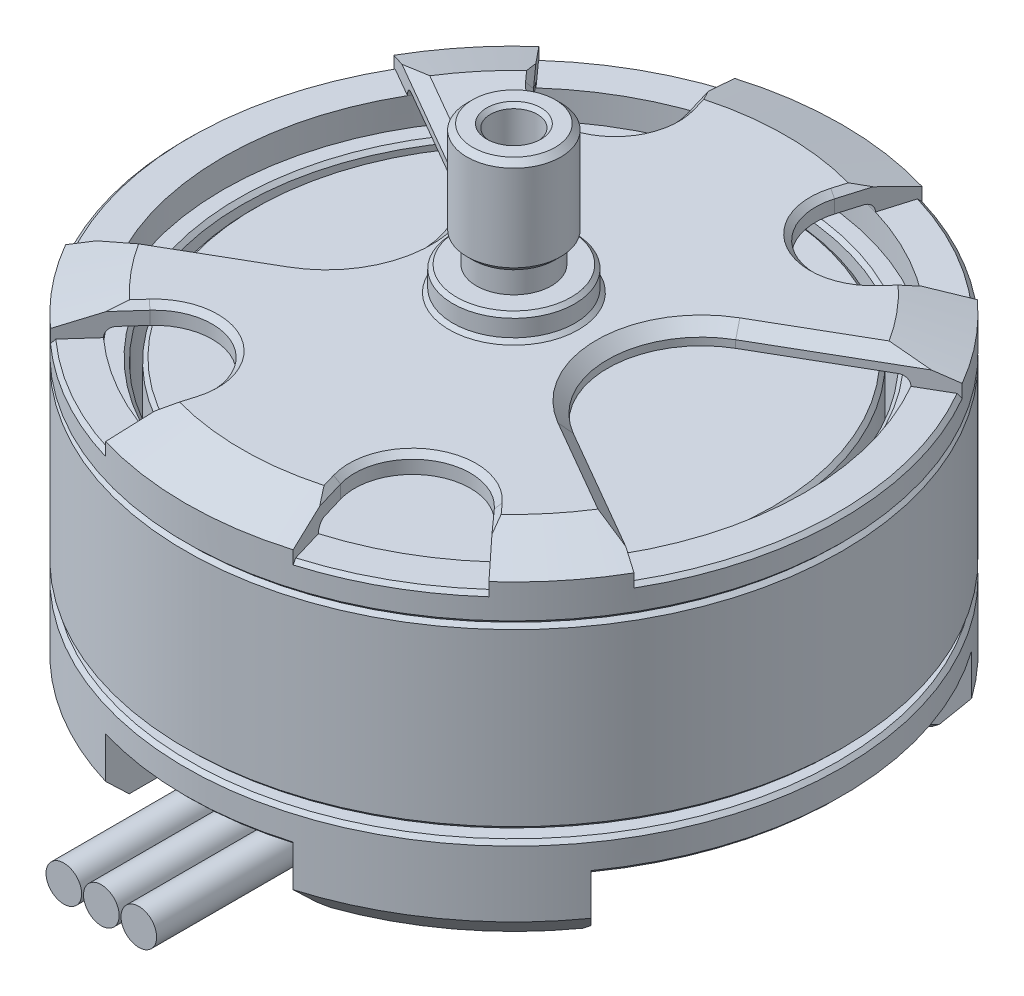
SolidWorks part; units mm, degrees
ref_plane "Front Plane" through (0, 0, 0) normal (0, 0, 1) x (1, 0, 0)
ref_plane "Top Plane" through (0, 0, 0) normal (0, 1, 0) x (1, 0, 0)
ref_plane "Right Plane" through (0, 0, 0) normal (1, 0, 0) x (0, 0, -1)
sketch "Sketch1" plane through (0, 0, 0) normal (0, 0, 1) x (1, 0, 0)
  line L0 (0.75, 0) -> (2, 0)
  line L1 (2, 0) -> (2, 2)
  line L2 (2, 2) -> (5, 2)
  line L3 (5, 2) -> (6, 0)
  line L4 (6, 0) -> (16, 0)
  line L5 (16, 0) -> (17.5, 1.5)
  line L6 (17.5, 1.5) -> (17.5, 5.2)
  line L8 (14, 6.2) -> (14, 15.2)
  line L9 (14, 15.2) -> (3.25, 15.2)
  line L10 (3.25, 15.2) -> (3.25, 17.2)
  line L13 (16, 5.7) -> (17.5, 5.7)
  line L14 (17.5, 5.7) -> (17.5, 17.2) construction
  line L15 (17.5, 17.2) -> (14.5, 18.2)
  line L16 (14.5, 18.2) -> (3.25, 18.2)
  line L17 (3.25, 18.2) -> (3.25, 19.5)
  line L18 (3.25, 19.5) -> (2, 19.5)
  line L20 (2.5, 26) -> (0, 26)
  line L21 (0, 26) -> (0, 18.2)
  line L22 (14, 6.2) -> (6.5, 6.2)
  line L23 (6.5, 6.2) -> (6.5, 3.2)
  line L24 (7.5, 2.2) -> (15, 2.2)
  line L25 (16, 3.2) -> (16, 5.2)
  line L26 (16, 5.2) -> (17.5, 5.2)
  line L27 (3.25, 17.2) -> (15, 17.2)
  line L28 (15.5, 16.7) -> (15.5, 15.2)
  line L29 (15.5, 15.2) -> (14.5, 15.2)
  line L30 (14.5, 15.2) -> (14.5, 6.2)
  line L31 (14.5, 6.2) -> (16, 6.2)
  line L32 (16, 6.2) -> (16, 5.7)
  line L33 (17.5, 17.2) -> (17.5, 15.4)
  line L34 (17.5, 15.4) -> (17.3, 15.2)
  line L35 (17.3, 15.2) -> (17.5, 15)
  line L36 (17.5, 15) -> (17.5, 5.7)
  line L37 (2.5, 26) -> (2.5, 20.8)
  line L38 (2.5, 20.8) -> (2, 20.8)
  line L39 (2, 20.8) -> (2, 19.5)
  line L40 (0, 18.2) -> (0.75, 18.2)
  line L41 (0.75, 18.2) -> (0.75, 0)
  arc A0 (15, 2.2) -> (16, 3.2) centre (15, 3.2) ccw
  arc A1 (15, 17.2) -> (15.5, 16.7) centre (15, 16.7) cw
  arc A2 (6.5, 3.2) -> (7.5, 2.2) centre (7.5, 3.2) ccw
  point P25 (-2, 0)
  point P27 (-2.5, 26)
  point P28 (-3.25, 19.5)
  point P29 (-14.5, 18.2)
  point P30 (-14, 6.2)
  point P31 (-17.5, 5.2)
  point P32 (-5, 2)
  point P46 (-6.5, 2.2)
  point P49 (6.5, 2.2)
  point P50 (-6, 0)
  point P56 (-2, 20.8)
  point P57 (-0.75, 18.2)
  dimension "D20" = 0.5
  dimension "D23" = 1
  dimension "D1" = 4
  dimension "D2" = 35
  dimension "D3" = 135
  dimension "D4" = 2
  dimension "D5" = 10
  dimension "D6" = 5.2
  dimension "D7" = 12.5
  dimension "D8" = 3
  dimension "D9" = 1
  dimension "D10" = 18.2
  dimension "D11" = 1.5
  dimension "D12" = 3
  dimension "D13" = 1
  dimension "D14" = 5
  dimension "D15" = 6.5
  dimension "D16" = 2
  dimension "D17" = 3
  dimension "D18" = 0.5
  dimension "D19" = 2.2
  dimension "D21" = 0.5
  dimension "D22" = 13
  dimension "D24" = 1.3
  dimension "D25" = 26
  dimension "D26" = 0.4
  dimension "D27" = 1.5
  dimension "D28" = 12
  dimension "D29" = 4
  dimension "D30" = 1.5
revolve "Revolve1" add sketch "Sketch1" angle 360 about L21
sketch "Sketch2" plane through (0, 0, 0) normal (0, -1, 0) x (1, 0, 0)
  line L0 (-5, 16.7705) -> (-5, 8.0777)
  line L2 (0, 0) -> (0, 17.5) construction
  line L3 (5, 16.7705) -> (5, 8.0777)
  line L4 (14.2539, 10.1527) -> (8.4475, 4.3463)
  line L5 (8.4475, -4.3463) -> (14.2539, -10.1527)
  line L6 (0, 0) -> (9.5, 0) construction
  line L7 (-4.3463, -8.4475) -> (-10.1527, -14.2539)
  line L8 (10.1527, -14.2539) -> (4.3463, -8.4475)
  line L9 (-8.4475, 4.3463) -> (-14.2539, 10.1527)
  line L10 (-14.2539, -10.1527) -> (-8.4475, -4.3463)
  line L11 (0, 0) -> (8.4475, -4.3463) construction
  line L12 (0, 0) -> (-4.3463, -8.4475) construction
  line L13 (12.3744, 12.3744) -> (-12.3744, -12.3744) construction
  line L14 (-12.3744, 12.3744) -> (12.3744, -12.3744) construction
  line L15 (-12.3744, 12.3744) -> (12.3744, 12.3744) construction
  circle A0 centre (0, 0) radius 17.5 construction
  arc A1 (5, 16.7705) -> (-5, 16.7705) centre (0, 0) ccw
  arc A2 (5, 8.0777) -> (-5, 8.0777) centre (0, 0) ccw
  arc A4 (8.4475, -4.3463) -> (8.4475, 4.3463) centre (0, 0) ccw
  arc A5 (14.2539, 10.1527) -> (14.2539, -10.1527) centre (0, 0) cw
  arc A6 (10.1527, -14.2539) -> (-10.1527, -14.2539) centre (0, 0) cw
  arc A7 (-4.3463, -8.4475) -> (4.3463, -8.4475) centre (0, 0) ccw
  arc A8 (-14.2539, -10.1527) -> (-14.2539, 10.1527) centre (0, 0) cw
  arc A9 (-8.4475, 4.3463) -> (-8.4475, -4.3463) centre (0, 0) ccw
  circle A10 centre (8.8388, 8.8388) radius 1.5
  circle A11 centre (6.7175, -6.7175) radius 1.5
  circle A12 centre (-8.8388, -8.8388) radius 1.5
  circle A13 centre (-6.7175, 6.7175) radius 1.5
  dimension "D2" = 9.5
  dimension "D6" = 3
  dimension "D1" = 10
  dimension "D4" = 90
  dimension "D5" = 5.8
  dimension "D7" = 25
  dimension "D8" = 19
  dimension "D3" = 3
extrude "Cut-Extrude4" cut sketch "Sketch2" against normal blind 3.5
fillet "Fillet1" radius 2 8 edges at (-4.3463, 1.1, -8.4475) (4.3463, 1.1, -8.4475) (-8.4475, 1.1, -4.3463) (-8.4475, 1.1, 4.3463) (8.4475, 1.1, -4.3463) (8.4475, 1.1, 4.3463) (-5, 1.1, 8.0777) (5, 1.1, 8.0777)
sketch "Sketch3" plane through (0, 18.2, 0) normal (0, 1, 0) x (1, 0, 0)
  line L0 (0, 17.5) -> (0, 0) construction
  line L1 (0, 0) -> (17.5, 0) construction
  line L2 (5, 16.7705) -> (3.927, 13.1716)
  line L3 (9.1822, 10.2274) -> (11.6911, 13.0218)
  line L4 (15.1554, 8.75) -> (7.5, 4.3301)
  line L5 (7.5, -4.3301) -> (15.1554, -8.75)
  line L6 (9.1822, -10.2274) -> (11.6911, -13.0218)
  line L7 (5, -16.7705) -> (3.927, -13.1716)
  line L8 (-9.1822, 10.2274) -> (-11.6911, 13.0218)
  line L9 (-5, 16.7705) -> (-3.927, 13.1716)
  line L10 (-7.5, -4.3301) -> (-15.1554, -8.75)
  line L11 (-15.1554, 8.75) -> (-7.5, 4.3301)
  line L12 (-9.1822, -10.2274) -> (-11.6911, -13.0218)
  line L13 (-5, -16.7705) -> (-3.927, -13.1716)
  line L14 (5.3765, 9.5965) -> (-5.3765, -9.5965) construction
  circle A0 centre (0, 0) radius 17.5 construction
  arc A1 (3.927, 13.1716) -> (9.1822, 10.2274) centre (6.8852, 12.2896) ccw
  arc A2 (7.5, 4.3301) -> (7.5, -4.3301) centre (10, 0) ccw
  arc A3 (15.1554, -8.75) -> (15.1554, 8.75) centre (0, 0) ccw
  arc A4 (11.6911, 13.0218) -> (5, 16.7705) centre (0, 0) ccw
  arc A5 (11.6911, -13.0218) -> (5, -16.7705) centre (0, 0) cw
  arc A6 (3.927, -13.1716) -> (9.1822, -10.2274) centre (6.8852, -12.2896) cw
  arc A7 (-11.6911, 13.0218) -> (-5, 16.7705) centre (0, 0) cw
  arc A8 (-3.927, 13.1716) -> (-9.1822, 10.2274) centre (-6.8852, 12.2896) cw
  arc A9 (-7.5, 4.3301) -> (-7.5, -4.3301) centre (-10, 0) cw
  arc A10 (-15.1554, -8.75) -> (-15.1554, 8.75) centre (0, 0) cw
  arc A11 (-3.927, -13.1716) -> (-9.1822, -10.2274) centre (-6.8852, -12.2896) ccw
  arc A12 (-11.6911, -13.0218) -> (-5, -16.7705) centre (0, 0) ccw
  dimension "D2" = 5
  dimension "D3" = 22
  dimension "D1" = 60
  dimension "D4" = 10
  dimension "D5" = 5.5
extrude "Cut-Extrude5" cut sketch "Sketch3" against normal blind 1.5
sketch "Sketch4" plane through (0, 26, 0) normal (0, 1, 0) x (1, 0, 0)
  circle A0 centre (0, 0) radius 1.25
  dimension "D1" = 2.5
extrude "Cut-Extrude6" cut sketch "Sketch4" against normal blind 3
chamfer "Chamfer1" distance 0.6 angle 45 6 edges at (-10.0287, 18.2, 5.7901) (-10.0287, 18.2, -5.7901) (-5, 18.2, 0) (10.0287, 18.2, -5.7901) (10.0287, 18.2, 5.7901) (5, 18.2, 0)
chamfer "Chamfer2" distance 0.3 angle 45 38 edges at (-11.2921, 0, -7.1909) (-11.2921, 0, 7.1909) (-8.8697, 0, -4.3284) (-8.8697, 0, 4.3284) (-9.5, 0, 0) (-5, 0, 13.1502) (5, 0, 13.1502) (-4.2158, 0, 9.5138) (4.2158, 0, 9.5138) (0, 0, 9.5) (11.2921, 0, 7.1909) (11.2921, 0, -7.1909) (8.8697, 0, 4.3284) (8.8697, 0, -4.3284) (9.5, 0, 0) (7.1909, 0, -11.2921) (-7.1909, 0, -11.2921) (4.3284, 0, -8.8697) (-4.3284, 0, -8.8697) (0, 0, -9.5) (8.2175, 0, -6.7175) (10.3388, 0, 8.8388) (-8.2175, 0, 6.7175) (-10.3388, 0, -8.8388) (-9.4346, 18.2, -10.5084) (-4.0349, 18.2, -13.5336) (-5.3765, 18.2, -9.5965) (-4.0349, 18.2, 13.5336) (-9.4346, 18.2, 10.5084) (-5.3765, 18.2, 9.5965) (9.4346, 18.2, 10.5084) (4.0349, 18.2, 13.5336) (5.3765, 18.2, 9.5965) (4.0349, 18.2, -13.5336) (9.4346, 18.2, -10.5084) (5.3765, 18.2, -9.5965) (-2.5, 26, 0) (-2.5, 20.8, 0)
chamfer "Chamfer3" distance 0.2 angle 45 6 edges at (-2, 0, 0) (-14, 6.2, 0) (-14, 15.2, 0) (-14.5, 15.2, 0) (-14.5, 6.2, 0) (-0.75, 0, 0)
ref_plane "Plane1" through (2, 0, 0) normal (1, 0, 0) x (0, 0, -1)
sketch "Sketch5" plane through (2, 0, 0) normal (1, 0, 0) x (0, 0, -1)
  line L0 (-6.9, 4.6) -> (-9.2, 4.6)
  line L1 (-10.6, 3.2) -> (-10.6, 2.3)
  line L2 (-12, 0.9) -> (-22, 0.9)
  line L3 (-6.9, 3.7) -> (-9.2, 3.7) construction
  line L4 (-9.7, 3.2) -> (-9.7, 2.3) construction
  line L5 (-12, 0) -> (-22, 0) construction
  line L6 (-7.7159, 4.6) -> (-9.2, 4.6) construction
  line L7 (-7.7159, 3.7) -> (-9.2, 3.7) construction
  line L8 (-6.9, 5.5) -> (-9.2, 5.5) construction
  line L9 (-11.5, 3.2) -> (-11.5, 2.3) construction
  line L10 (-12, 1.8) -> (-22, 1.8) construction
  line L11 (-6.9, 4.6) -> (-9.2, 4.6) construction
  line L12 (-16, 5.7) -> (16, 5.7) construction
  line L13 (-6.9, 5.5) -> (-6.9, 3.7) construction
  line L14 (-9.1711, 2.2) -> (-9.5, 2.2) construction
  line L15 (-6.5, 6.2) -> (6.5, 6.2) construction
  line L16 (-6.5, 6.2) -> (6.5, 6.2) construction
  line L17 (-9.1711, 2.2) -> (-9.5, 2.2) construction
  line L18 (-15.0967, 0) -> (-9.3249, 0) construction
  line L19 (-15.0967, 0) -> (-9.3249, 0) construction
  arc A0 (-9.2, 4.6) -> (-10.6, 3.2) centre (-9.2, 3.2) ccw
  arc A1 (-10.6, 2.3) -> (-12, 0.9) centre (-12, 2.3) cw
  arc A2 (-9.2, 3.7) -> (-9.7, 3.2) centre (-9.2, 3.2) ccw construction
  arc A3 (-9.7, 2.3) -> (-12, 0) centre (-12, 2.3) cw construction
  arc A4 (-9.2, 5.5) -> (-11.5, 3.2) centre (-9.2, 3.2) ccw construction
  arc A5 (-11.5, 2.3) -> (-12, 1.8) centre (-12, 2.3) cw construction
  point P39 (-6.9, 4.6)
  dimension "D5" = 0.5
  dimension "D3" = 0.2
  dimension "D4" = 0.2
  dimension "D6" = 10
  dimension "D7" = 0.4
  dimension "D1" = 0.9
  dimension "D2" = 0.9
sweep "Sweep1" add path "Sketch5" circular profile diameter 1.9 parameters "D3"=1.9
pattern_linear "LPattern2" count 3 spacing 2 along (-1, 0, 0) of bodies 105
